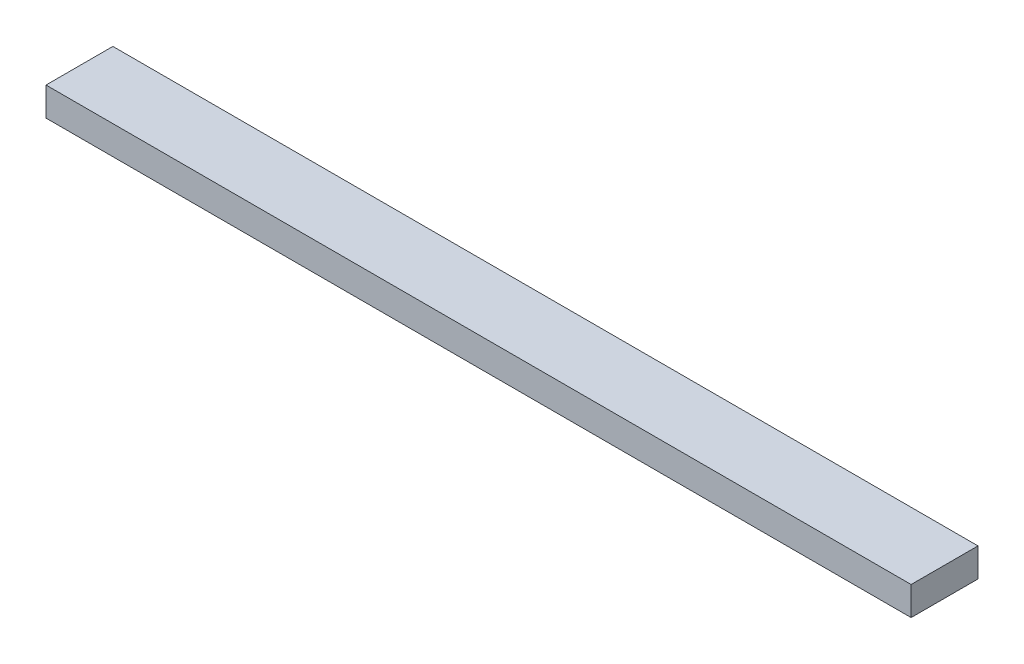
SolidWorks part; units mm, degrees
ref_plane "Front Plane" through (0, 0, 0) normal (0, 0, 1) x (1, 0, 0)
ref_plane "Top Plane" through (0, 0, 0) normal (0, 1, 0) x (1, 0, 0)
ref_plane "Right Plane" through (0, 0, 0) normal (1, 0, 0) x (0, 0, -1)
sketch "Sketch1" plane through (0, 0, 0) normal (0, 1, 0) x (1, 0, 0)
  line L0 (0, 0) -> (1150, 0)
  line L1 (1150, 0) -> (1150, -88.9)
  line L2 (1150, -88.9) -> (0, -88.9)
  line L3 (0, -88.9) -> (0, 0)
  dimension "D1" = 1150
  dimension "D2" = 90
  dimension "D3" = 90
  dimension "D4" = 88.9
extrude "Boss-Extrude1" add sketch "Sketch1" along normal blind 38.1
